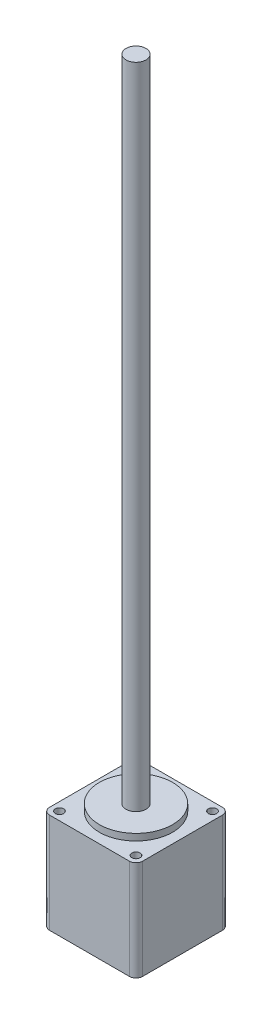
SolidWorks part; units mm, degrees
ref_plane "Front Plane" through (0, 0, 0) normal (0, 0, 1) x (1, 0, 0)
ref_plane "Top Plane" through (0, 0, 0) normal (0, 1, 0) x (1, 0, 0)
ref_plane "Right Plane" through (0, 0, 0) normal (1, 0, 0) x (0, 0, -1)
sketch "Sketch1" plane through (0, 0, 0) normal (0, 1, 0) x (1, 0, 0)
  line L0 (2.5, 2.5) -> (2.5, 25.5) construction
  line L1 (0, 0) -> (28, 0)
  line L2 (0, 0) -> (0, 28)
  line L3 (0, 28) -> (28, 28)
  line L4 (28, 0) -> (28, 28)
  line L5 (2.5, 25.5) -> (25.5, 25.5) construction
  line L6 (25.5, 2.5) -> (25.5, 25.5) construction
  line L7 (2.5, 2.5) -> (25.5, 2.5) construction
  circle A0 centre (2.5, 25.5) radius 1.25
  circle A1 centre (2.5, 2.5) radius 1.25
  circle A2 centre (25.5, 2.5) radius 1.25
  circle A3 centre (25.5, 25.5) radius 1.25
  dimension "D3" = 2.5
  dimension "D1" = 28
  dimension "D2" = 2.5
extrude "Boss-Extrude1" add sketch "Sketch1" along normal blind 30
sketch "Sketch2" plane through (0, 30, 0) normal (0, 1, 0) x (1, 0, 0)
  line L0 (14, 28) -> (14, 0) construction
  line L1 (28, 28) -> (0, 28) construction
  line L2 (0, 0) -> (28, 0) construction
  circle A0 centre (14, 14) radius 11
  dimension "D1" = 22
extrude "Boss-Extrude2" add sketch "Sketch2" along normal blind 2
sketch "Sketch3" plane through (0, 32, 0) normal (0, 1, 0) x (1, 0, 0)
  circle A0 centre (14, 14) radius 3
  dimension "D1" = 6
extrude "Boss-Extrude3" add sketch "Sketch3" along normal blind 195
fillet "Fillet1" radius 2 4 edges at (0, 15, -28) (28, 15, -28) (0, 15, 0) (28, 15, 0)
